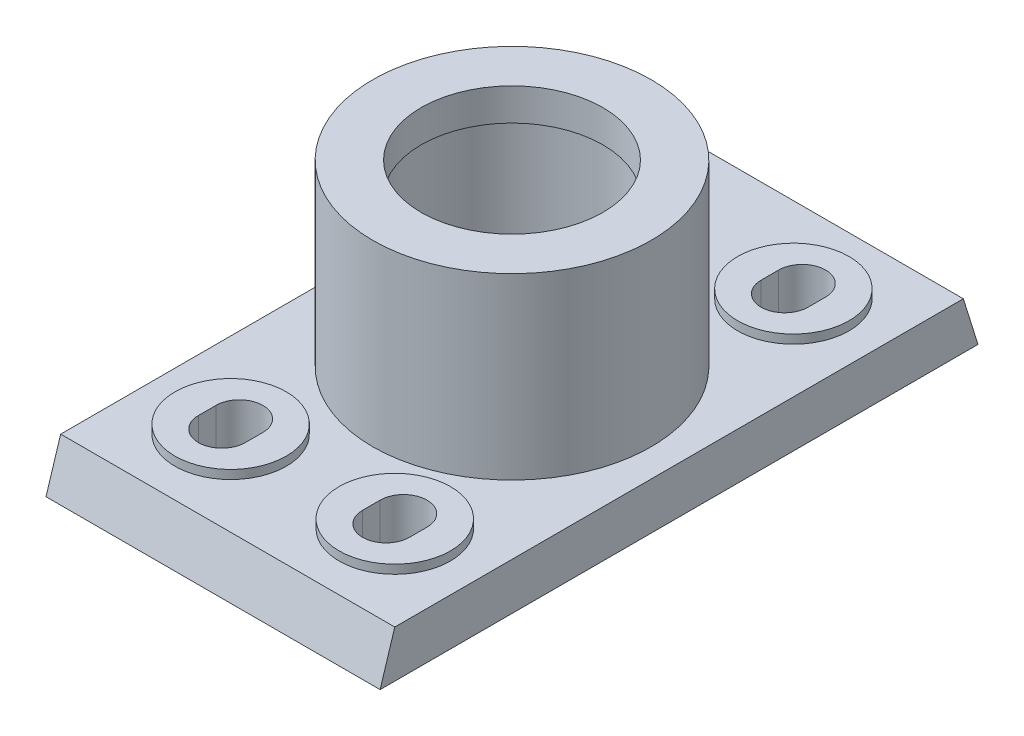
SolidWorks part; units mm, degrees
ref_plane "Front Plane" through (0, 0, 0) normal (0, 0, 1) x (1, 0, 0)
ref_plane "Top Plane" through (0, 0, 0) normal (0, 1, 0) x (1, 0, 0)
ref_plane "Right Plane" through (0, 0, 0) normal (1, 0, 0) x (0, 0, -1)
sketch "Sketch1" plane through (0, 0, 0) normal (1, 0, 0) x (0, 0, -1)
  line L0 (0, 24.8193) -> (0, -56.8193) construction
  line L1 (-102, -16) -> (102, -16)
  line L2 (102, -16) -> (97, 0)
  line L3 (97, 0) -> (-97, 0)
  line L4 (-102, -16) -> (-97, 0)
  point P8 (0, -16)
  point P9 (0, 0)
  dimension "D1" = 102
  dimension "D2" = 16
  dimension "D3" = 5
extrude "Boss-Extrude2" add sketch "Sketch1" along normal mid plane 114
sketch "Sketch3" plane through (0, 0, 0) normal (0, 1, 0) x (1, 0, 0)
  circle A0 centre (0, 0) radius 31
  circle A1 centre (0, 0) radius 47.5
  dimension "D2" = 95
  dimension "D3" = 62
  dimension "D1" = 0
extrude "Boss-Extrude3" add sketch "Sketch3" along normal blind 13
ref_plane "Plane1" through (0, 13, 0) normal (0, 1, 0) x (1, 0, 0)
sketch "Sketch4" plane through (0, 13, 0) normal (0, 1, 0) x (1, 0, 0)
  circle A0 centre (0, 0) radius 32.5
  circle A1 centre (0, 0) radius 47.5
  dimension "D1" = 65
  dimension "D2" = 95
extrude "Boss-Extrude4" add sketch "Sketch4" along normal blind 37
ref_plane "Plane2" through (0, 50, 0) normal (0, 1, 0) x (1, 0, 0)
sketch "Sketch5" plane through (0, 50, 0) normal (0, 1, 0) x (1, 0, 0)
  circle A0 centre (0, 0) radius 31
  circle A1 centre (0, 0) radius 47.5
  dimension "D1" = 62
  dimension "D2" = 95
extrude "Boss-Extrude5" add sketch "Sketch5" along normal blind 11
sketch "Sketch6" plane through (0, -16, 0) normal (0, -1, 0) x (1, 0, 0)
  line L0 (60.1041, 0) -> (-77.228, 0) construction
  line L1 (47, 92) -> (-47, 92)
  line L2 (47, 92) -> (47, 6.5)
  line L3 (47, 6.5) -> (-47, 6.5)
  line L4 (-47, 92) -> (-47, 6.5)
  line L5 (57, 102) -> (-57, 102) construction
  line L6 (57, 102) -> (57, -102) construction
  line L7 (-57, 102) -> (-57, -102) construction
  line L8 (47, -6.5) -> (-47, -6.5)
  line L9 (-47, -92) -> (-47, -6.5)
  line L10 (47, -92) -> (-47, -92)
  line L11 (47, -92) -> (47, -6.5)
  dimension "D1" = 6.5
  dimension "D2" = 10
  dimension "D3" = 10
  dimension "D4" = 10
extrude "Cut-Extrude1" cut sketch "Sketch6" against normal blind 3
sketch "Sketch7" plane through (0, 0, 0) normal (0, 1, 0) x (1, 0, 0)
  line L0 (-57, 97) -> (-57, -97) construction
  line L2 (57, -97) -> (-57, -97) construction
  line L3 (57, 97) -> (57, -97) construction
  line L4 (-64.6372, 0) -> (76.1257, 0) construction
  circle A0 centre (-28, -68) radius 19
  circle A1 centre (28, -68) radius 19
  circle A2 centre (28, 68) radius 19
  circle A3 centre (-28, 68) radius 19
  dimension "D1" = 38
  dimension "D2" = 38
  dimension "D3" = 29
  dimension "D5" = 29
  dimension "D6" = 29
  dimension "D4" = 29
extrude "Boss-Extrude6" add sketch "Sketch7" along normal blind 3
sketch "Sketch8" plane through (0, 3, 0) normal (0, 1, 0) x (1, 0, 0)
  line L0 (28, -65) -> (28, -71) construction
  line L1 (36, -65) -> (36, -71)
  line L2 (20, -65) -> (20, -71)
  line L3 (57, 97) -> (57, -97) construction
  line L4 (-67.3078, 0) -> (101.0629, 0) construction
  line L5 (-28, -65) -> (-28, -71) construction
  line L6 (-36, -65) -> (-36, -71)
  line L7 (-20, -65) -> (-20, -71)
  line L8 (28, 65) -> (28, 71) construction
  line L9 (36, 65) -> (36, 71)
  line L10 (20, 65) -> (20, 71)
  line L11 (-28, 65) -> (-28, 71) construction
  line L12 (-36, 65) -> (-36, 71)
  line L13 (-20, 65) -> (-20, 71)
  arc A0 (36, -65) -> (20, -65) centre (28, -65) ccw
  arc A1 (20, -71) -> (36, -71) centre (28, -71) ccw
  circle A3 centre (28, -68) radius 19 construction
  arc A4 (36, 65) -> (20, 65) centre (28, 65) cw
  arc A5 (-36, -65) -> (-20, -65) centre (-28, -65) cw
  arc A6 (-20, -71) -> (-36, -71) centre (-28, -71) cw
  circle A7 centre (-28, -68) radius 19 construction
  arc A8 (20, 71) -> (36, 71) centre (28, 71) cw
  arc A9 (-36, 65) -> (-20, 65) centre (-28, 65) ccw
  arc A10 (-20, 71) -> (-36, 71) centre (-28, 71) ccw
  point P2 (28, -68)
  point P17 (-28, -68)
  point P26 (28, 68)
  point P33 (-28, 68)
  dimension "D2" = 22
  dimension "D6" = 22
  dimension "D1" = 16
  dimension "D3" = 0
  dimension "D4" = 0
  dimension "D5" = 6
extrude "Cut-Extrude2" cut sketch "Sketch8" against normal through all
sketch "Sketch9" plane through (0, 0, 0) normal (0, 1, 0) x (1, 0, 0)
  circle A0 centre (-22, 0) radius 1.5
  dimension "D2" = 3
  dimension "D1" = 22
extrude "Cut-Extrude3" cut sketch "Sketch9" against normal blind 5
